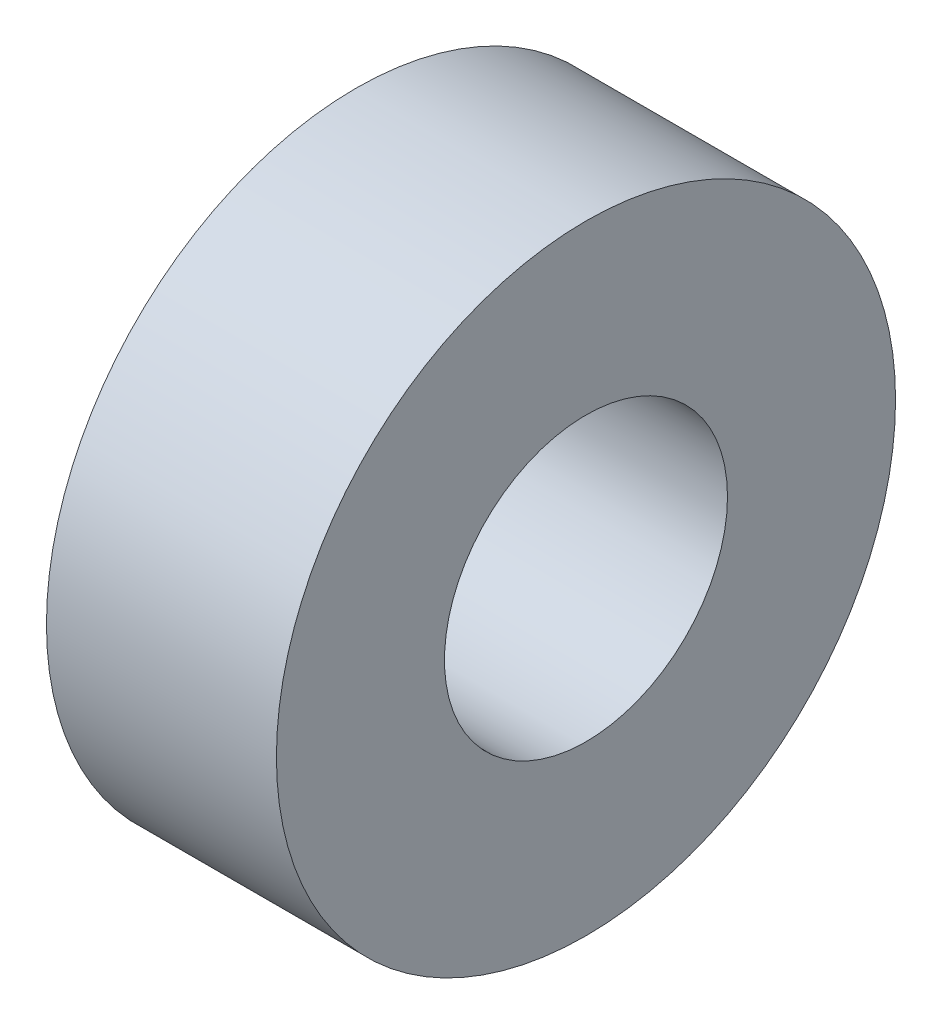
SolidWorks part; units mm, degrees
ref_plane "Front Plane" through (0, 0, 0) normal (0, 0, 1) x (1, 0, 0)
ref_plane "Top Plane" through (0, 0, 0) normal (0, 1, 0) x (1, 0, 0)
ref_plane "Right Plane" through (0, 0, 0) normal (1, 0, 0) x (0, 0, -1)
sketch "Sketch1" plane through (0, 0, 0) normal (1, 0, 0) x (0, 0, -1)
  circle A0 centre (0, 0) radius 3.5
  circle A1 centre (0, 0) radius 1.6
  dimension "D1" = 7
  dimension "D2" = 3.2
extrude "Boss-Extrude1" add sketch "Sketch1" along normal blind 2.6
